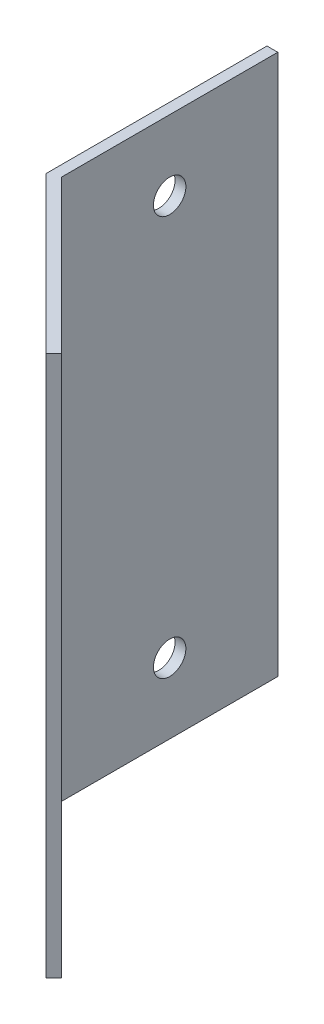
SolidWorks part; units mm, degrees
ref_plane "Face" through (0, 0, 0) normal (0, 0, 1) x (1, 0, 0)
ref_plane "Dessus" through (0, 0, 0) normal (0, 1, 0) x (1, 0, 0)
ref_plane "Droite" through (0, 0, 0) normal (1, 0, 0) x (0, 0, -1)
sketch "Esquisse1" plane through (0, 0, 0) normal (0, 1, 0) x (1, 0, 0)
  line L0 (0, 0) -> (0, 20.4142)
  line L1 (0, 20.4142) -> (1, 20.4142)
  line L2 (1, 20.4142) -> (1, 0.4142)
  line L3 (1, 0.4142) -> (15.1421, -13.7279)
  line L4 (15.1421, -13.7279) -> (14.435, -14.435)
  line L5 (14.435, -14.435) -> (0, 0)
  dimension "D1" = 1
  dimension "D2" = 1
  dimension "D3" = 45
  dimension "D4" = 20
extrude "Extrusion1" add sketch "Esquisse1" along normal blind 50
sketch "Esquisse2" plane through (1, 0, 0) normal (1, 0, 0) x (0, 0, -1)
  line L0 (0.4142, 25) -> (20.4142, 25) construction
  line L1 (0.4142, 50) -> (0.4142, 0) construction
  line L2 (20.4142, 50) -> (20.4142, 0) construction
  line L3 (10.4142, 0) -> (10.4142, 50) construction
  line L4 (0.4142, 0) -> (20.4142, 0) construction
  line L5 (0.4142, 50) -> (20.4142, 50) construction
  circle A0 centre (10.4142, 6.5) radius 1.5
  circle A2 centre (10.4142, 43.5) radius 1.5
  dimension "D1" = 3
  dimension "D2" = 18.5
extrude "Extrusion2" cut sketch "Esquisse2" against normal up to next
sketch "Esquisse3" plane through (0.7071, 0, -0.7071) normal (0.7071, 0, -0.7071) x (-0.7071, 0, -0.7071)
  line L0 (-10.4142, 50) -> (-10.4142, 0) construction
  line L1 (-20.4142, 50) -> (-0.4142, 50) construction
  line L2 (-20.4142, 0) -> (-0.4142, 0) construction
  line L3 (-20.4142, 25) -> (-0.4142, 25) construction
  line L4 (-20.4142, 50) -> (-20.4142, 0) construction
  line L5 (-0.4142, 50) -> (-0.4142, 0) construction
  circle A0 centre (-10.4142, 43.5) radius 1.5
  circle A3 centre (-10.4142, 6.5) radius 1.5
  dimension "D1" = 3
  dimension "D2" = 18.5
extrude "Extrusion3" cut sketch "Esquisse3" against normal up to next
